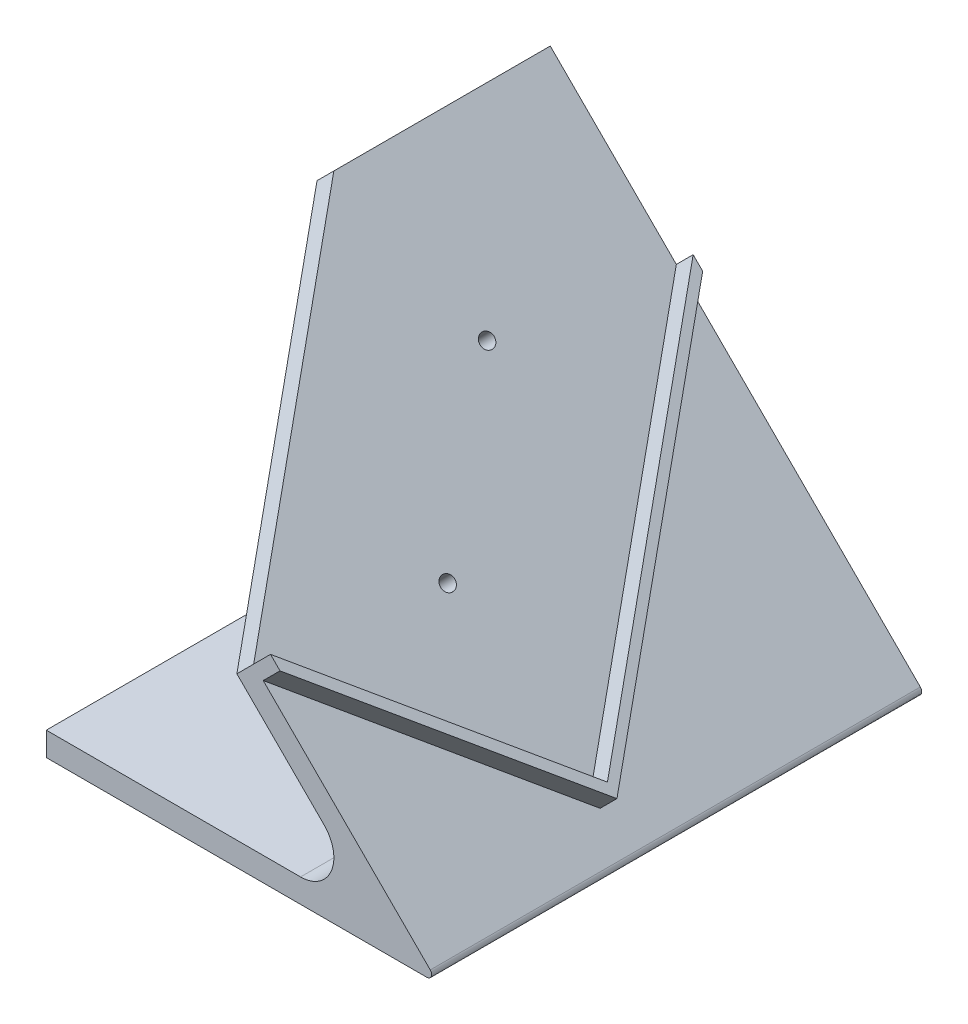
SolidWorks part; units mm, degrees
ref_plane "Ebene vorne" through (0, 0, 0) normal (0, 0, 1) x (1, 0, 0)
ref_plane "Ebene oben" through (0, 0, 0) normal (0, 1, 0) x (1, 0, 0)
ref_plane "Ebene rechts" through (0, 0, 0) normal (1, 0, 0) x (0, 0, -1)
sketch "Sketch1" plane through (0, 0, 0) normal (0, 0, 1) x (1, 0, 0)
  line L0 (2.9254, 74.4889) -> (80.7071, -3.2929)
  line L1 (80, -5) -> (0, -5)
  line L2 (0, -5) -> (0, 0)
  line L3 (0, 0) -> (53.4437, 0)
  line L4 (2.9254, 74.4889) -> (-0.6102, 70.9533)
  line L5 (58.3934, 11.9497) -> (-0.6102, 70.9533)
  arc A0 (80.7071, -3.2929) -> (80, -5) centre (80, -4) cw
  arc A1 (53.4437, 0) -> (58.3934, 11.9497) centre (53.4437, 7) ccw
  dimension "D5" = 7
  dimension "D6" = 1
  dimension "D1" = 5
  dimension "D2" = 45
  dimension "D3" = 80
  dimension "D4" = 110
extrude "Boss-Extrude1" add sketch "Sketch1" along normal blind 103
sketch "Sketch2" plane through (38.7071, 38.7071, 0) normal (0.7071, 0.7071, 0) x (0, 0, -1)
  line L0 (-100.4092, -9.501) -> (-103, -6.9102)
  line L1 (-1.4142, 11.7122) -> (-40.3051, 50.603)
  line L2 (-40.3051, 50.603) -> (-100.4092, -9.501)
  line L3 (-100.4092, -9.501) -> (-61.5183, -48.3919)
  line L4 (-61.5183, -48.3919) -> (-1.4142, 11.7122)
  line L5 (-103, 50.603) -> (0, 50.603) construction
  line L7 (-103, -59.397) -> (-103, 50.603) construction
  line L8 (-103, -9.7386) -> (-61.5183, -51.2203)
  line L9 (-61.5183, -51.2203) -> (0, 10.2979)
  line L10 (0, -59.397) -> (0, 50.603) construction
  line L11 (-1.4142, 11.7122) -> (0, 13.1264)
  line L12 (-103, -6.9102) -> (-103, -9.7386)
  dimension "D1" = 55
  dimension "D2" = 85
  dimension "D3" = 45
  dimension "D4" = 2
  dimension "D6" = 2
extrude "Boss-Extrude2" add sketch "Sketch2" along normal blind 5
ref_plane "Plane1" through (-33.9729, 33.9729, 48.0449) normal (-0.5, 0.5, 0.7071) x (0.866, 0.2887, 0.4082)
sketch "Sketch3" plane through (-33.9729, 33.9729, 48.0449) normal (-0.5, 0.5, 0.7071) x (0.866, 0.2887, 0.4082)
  line L0 (89.5658, -31.8525) -> (85.4833, -34.7392)
  line L1 (62.0036, -1.5339) -> (96.0693, -49.7101) construction
  line L2 (93.6483, -28.9657) -> (89.5658, -31.8525) construction
sketch "Sketch4" plane through (38.7071, 38.7071, 0) normal (0.7071, 0.7071, 0) x (0, 0, -1)
  line L0 (-103, -6.9102) -> (-45.4868, 50.603)
  line L1 (-103, 50.603) -> (0, 50.603) construction
extrude "Cut-Extrude1" cut sketch "Sketch4" against normal blind 5 and the other way through all
hole_wizard "M5 Clearance Hole1" positions "Sketch5" profile "Sketch6" hole
sketch "Sketch5" plane through (80.6288, -3.2145, 114.5985) normal (0.7071, 0.7071, 0) x (-0.5, 0.5, 0.7071)
  line L2 (-0.83, -129.2368) -> (-0.83, -49.2368) construction
  point P0 (-0.83, -69.2368)
  point P1 (-0.83, -109.2368)
sketch "Sketch6" plane through (46.4254, 30.9889, 65.0538) normal (0, 0, 1) x (-0.7071, 0.7071, 0)
  line L0 (0, 0) -> (0, 4.999)
  line L1 (0, 4.999) -> (1.5, 4.999)
  line L2 (1.5, 4.999) -> (1.5, 0)
  line L3 (1.5, 0) -> (0, 0)
  line L4 (0, -6.35) -> (0, 107.95) construction
  dimension "Thru Hole Dia." = 3
  dimension "Thru Hole Depth" = 4.999
